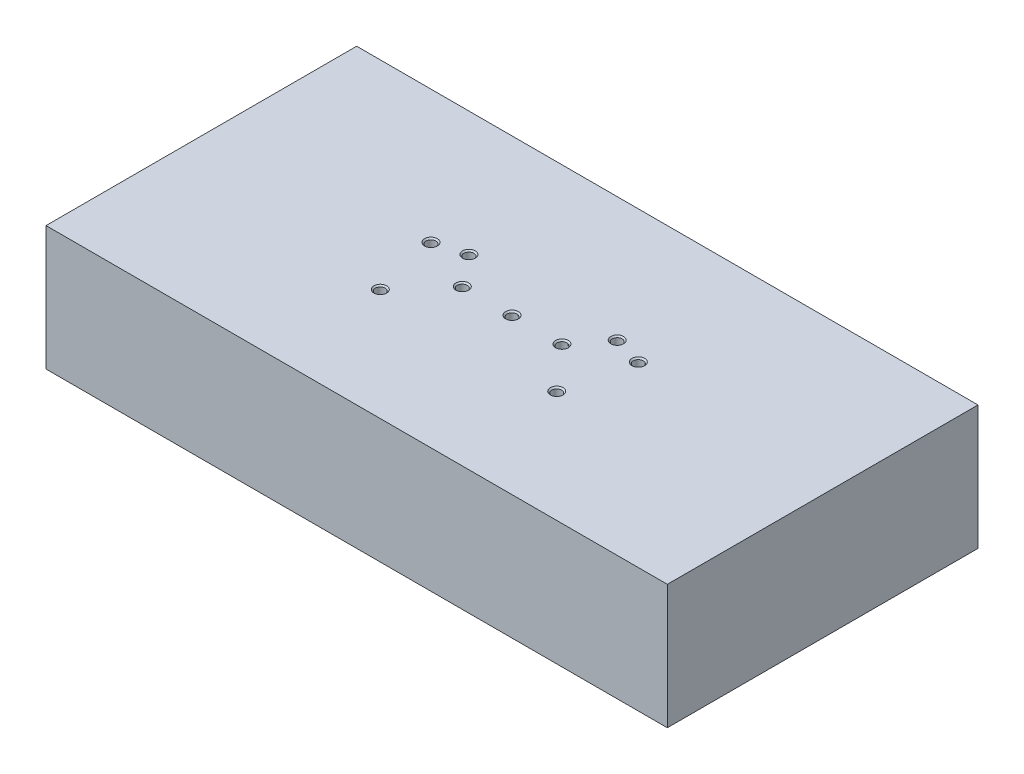
SolidWorks part; units mm, degrees
ref_plane "Front Plane" through (0, 0, 0) normal (0, 0, 1) x (1, 0, 0)
ref_plane "Top Plane" through (0, 0, 0) normal (0, 1, 0) x (1, 0, 0)
ref_plane "Right Plane" through (0, 0, 0) normal (1, 0, 0) x (0, 0, -1)
sketch "Sketch1" plane through (0, 0, 0) normal (0, 1, 0) x (1, 0, 0)
  line L0 (0, 0) -> (0, -50000) construction
  line L1 (0, 0) -> (50000, 0) construction
  line L23 (0, 1.012) -> (0, -6863.9387) construction
  line L24 (-50, -25) -> (50, -25)
  line L25 (-50, -25) -> (-50, 25)
  line L26 (-50, 25) -> (50, 25)
  line L27 (50, -25) -> (50, 25)
  line L28 (-50, -25) -> (50, 25) construction
  line L29 (-50, 25) -> (50, -25) construction
  line L30 (0.8079, 0) -> (6865.7586, 0) construction
  line L32 (-11.7, 3) -> (-0.25, 3)
  line L33 (-11.7, 3) -> (-11.7, -3)
  line L34 (-11.7, -3) -> (11.7, -3)
  line L35 (11.7, 3) -> (11.7, -3)
  line L41 (-0.25, 7) -> (-0.25, 3)
  line L42 (0.25, 7) -> (0.25, 3)
  line L44 (0.25, 3) -> (11.7, 3)
  line L46 (-0.25, 7) -> (0.25, 7)
  circle A18 centre (-14.2, -7) radius 0.5
  circle A19 centre (14.2, -7) radius 0.5
  circle A20 centre (-16.6851, 3.6435) radius 0.5
  circle A21 centre (16.6851, 3.6435) radius 0.5
  circle A22 centre (-11.9351, 5) radius 0.5
  circle A23 centre (11.9351, 5) radius 0.5
  point P6 (0, 0)
  point P41 (0, 0)
  dimension "D4" = 3.6435
  dimension "D5" = 5
  dimension "D6" = 7
  dimension "D7" = 4
  dimension "D11" = 1
  dimension "D15" = 2.5
  dimension "D16" = 1
  dimension "D19" = 1
  dimension "D12" = 1
  dimension "D22" = 1
  dimension "D2" = 6
  dimension "D13" = 28.4
  dimension "D17" = 100
  dimension "D18" = 50
  dimension "D21" = 4.75
  dimension "D24" = 0.5
  dimension "D31" = 23.8702
extrude "Boss-Extrude6" add sketch "Sketch1" along normal blind 10
sketch "Sketch3" plane through (0, 10, 0) normal (0, 1, 0) x (1, 0, 0)
  line L1 (-50, 25) -> (50, 25)
  line L2 (-50, 25) -> (-50, -25)
  line L3 (-50, -25) -> (50, -25)
  line L4 (50, 25) -> (50, -25)
  line L5 (-50, 25) -> (50, -25) construction
  line L6 (-50, -25) -> (50, 25) construction
  point P0 (0, 0)
extrude "Boss-Extrude7" add sketch "Sketch3" along normal blind 10
hole_wizard "M2 Tapped Hole1" positions "Sketch5" profile "Sketch6" tap size "M2" standard "ISO"
sketch "Sketch5" plane through (0, 20, 0) normal (0, 1, 0) x (1, 0, 0)
  point P0 (-16.6851, 3.6435)
  point P3 (-11.9351, 5)
  point P6 (11.9351, 5)
  point P9 (16.6851, 3.6435)
  point P12 (14.2, -7)
  point P15 (-14.2, -7)
  point P18 (-8, 0)
  point P20 (8.0426, 0)
  point P23 (-8, 0)
  point P25 (8.0426, 0)
  point P27 (0, 0)
  dimension "D1" = 8
sketch "Sketch6" plane through (-16.6851, 20, -3.6435) normal (1, 0, 0) x (0, 0, 1)
  line L0 (0, 0) -> (0, 20.4807)
  line L1 (0, 20.4807) -> (0.8, 20)
  line L2 (0.8, 20) -> (0.8, 0.225)
  line L3 (0.8, 0.225) -> (1.025, 0)
  line L5 (1.025, 0) -> (0, 0)
  line L6 (-0.8, 0.225) -> (-1.025, 0) construction
  line L10 (0, 20.4807) -> (-0.8, 20) construction
  line L11 (0, -6.35) -> (0, 107.95) construction
  dimension "Tap Drill Dia." = 1.6
  dimension "Tap Drill Depth" = 20
  dimension "Near C'Sink Dia." = 2.05
  dimension "Near C'Sink Angle" = 90
  dimension "Drill Angle" = 118
cosmetic thread "Hole Thread1"
cosmetic thread "Hole Thread2"
cosmetic thread "Hole Thread3"
cosmetic thread "Hole Thread4"
cosmetic thread "Hole Thread5"
cosmetic thread "Hole Thread6"
cosmetic thread "Hole Thread7"
cosmetic thread "Hole Thread8"
cosmetic thread "Hole Thread9"
cosmetic thread "Hole Thread10"
cosmetic thread "Hole Thread11"
